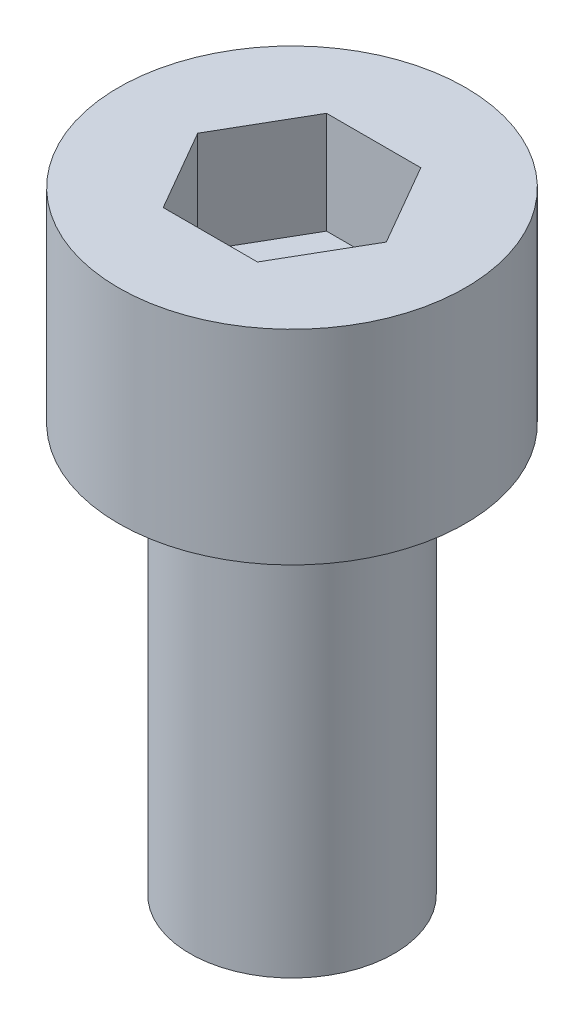
SolidWorks part; units mm, degrees
material "AISI 304"
ref_plane "前视基准面" through (0, 0, 0) normal (0, 0, 1) x (1, 0, 0)
ref_plane "上视基准面" through (0, 0, 0) normal (0, 1, 0) x (1, 0, 0)
ref_plane "右视基准面" through (0, 0, 0) normal (1, 0, 0) x (0, 0, -1)
sketch "草图1" plane through (0, 0, 0) normal (0, 1, 0) x (1, 0, 0)
  circle A0 centre (0, 0) radius 4.25
  dimension "D1" = 8.5
extrude "凸台-拉伸1" add sketch "草图1" along normal blind 5
sketch "草图2" plane through (0, 5, 0) normal (0, 1, 0) x (1, 0, 0)
  line L1 (2.3094, 0) -> (1.1547, 2)
  line L2 (1.1547, 2) -> (-1.1547, 2)
  line L3 (-1.1547, 2) -> (-2.3094, 0)
  line L4 (-2.3094, 0) -> (-1.1547, -2)
  line L5 (-1.1547, -2) -> (1.1547, -2)
  line L6 (1.1547, -2) -> (2.3094, 0)
  circle A0 centre (0, 0) radius 2 construction
  dimension "D1" = 4
extrude "切除-拉伸1" cut sketch "草图2" against normal blind 2.5
sketch "草图3" plane through (0, 0, 0) normal (0, -1, 0) x (1, 0, 0)
  circle A0 centre (0, 0) radius 2.5
  dimension "D1" = 5
extrude "凸台-拉伸2" add sketch "草图3" along normal blind 10
